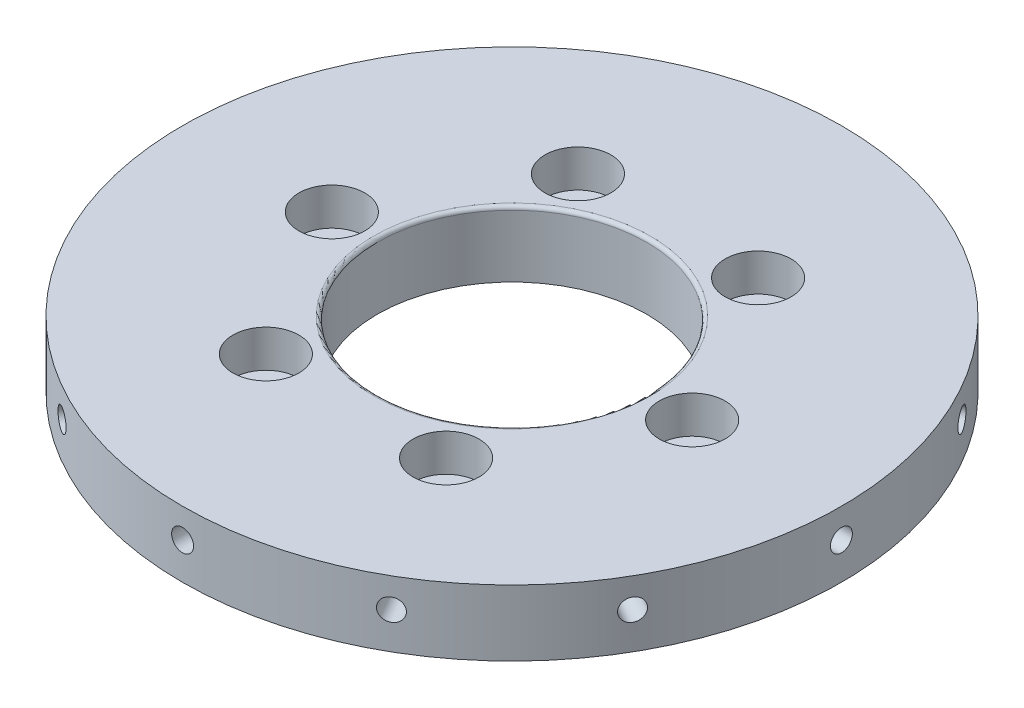
SolidWorks part; units mm, degrees
material "6061 合金"
ref_plane "前视基准面" through (0, 0, 0) normal (0, 0, 1) x (1, 0, 0)
ref_plane "上视基准面" through (0, 0, 0) normal (0, 1, 0) x (1, 0, 0)
ref_plane "右视基准面" through (0, 0, 0) normal (1, 0, 0) x (0, 0, -1)
sketch "草图1" plane through (0, 0, 0) normal (0, 1, 0) x (1, 0, 0)
  circle A0 centre (0, 0) radius 45
  circle A1 centre (0, 0) radius 24.6 construction
  circle A2 centre (-24.6, 0) radius 2.5
  circle A3 centre (-12.3, 21.3042) radius 2.5
  circle A4 centre (12.3, 21.3042) radius 2.5
  circle A5 centre (24.6, 0) radius 2.5
  circle A6 centre (12.3, -21.3042) radius 2.5
  circle A7 centre (-12.3, -21.3042) radius 2.5
  circle A8 centre (0, 0) radius 18.4
  point P19 (0, 0)
  dimension "D1" = 6
  dimension "D2" = 90
extrude "凸台-拉伸1" add sketch "草图1" along normal blind 9
sketch "草图2" plane through (0, 0, 0) normal (0, -1, 0) x (1, 0, 0)
  circle A0 centre (0, 0) radius 24.6 construction
  circle A1 centre (-21.3042, -12.3) radius 4
  circle A2 centre (0, 24.6) radius 4
  circle A3 centre (21.3042, -12.3) radius 4
  point P17 (0, 0)
  dimension "D1" = 3
extrude "切除-拉伸1" cut sketch "草图2" against normal blind 3
sketch "草图4" plane through (0, 9, 0) normal (0, 1, 0) x (1, 0, 0)
  circle A0 centre (-24.6, 0) radius 4.5
  circle A1 centre (0, 0) radius 24.6 construction
  circle A2 centre (-12.3, 21.3042) radius 4.5
  circle A3 centre (12.3, 21.3042) radius 4.5
  circle A4 centre (24.6, 0) radius 4.5
  circle A5 centre (12.3, -21.3042) radius 4.5
  circle A6 centre (-12.3, -21.3042) radius 4.5
  point P16 (0, 0)
  dimension "D1" = 6
extrude "切除-拉伸2" cut sketch "草图4" against normal blind 5.1
ref_plane "基准面1" through (45, 0, 0) normal (1, 0, 0) x (0, 0, -1)
sketch "草图5" plane through (45, 0, 0) normal (1, 0, 0) x (0, 0, -1)
  circle A0 centre (0, 5) radius 1.5
  point P2 (0, 0)
extrude "切除-拉伸3" cut sketch "草图5" against normal blind 10
pattern_circular "阵列(圆周)1" count 12 every 30 about axis through (0, 0, 0) along (0, 1, 0) of "切除-拉伸3"
fillet "圆角1" radius 0.5 1 edges at (0, 9, 18.4)
